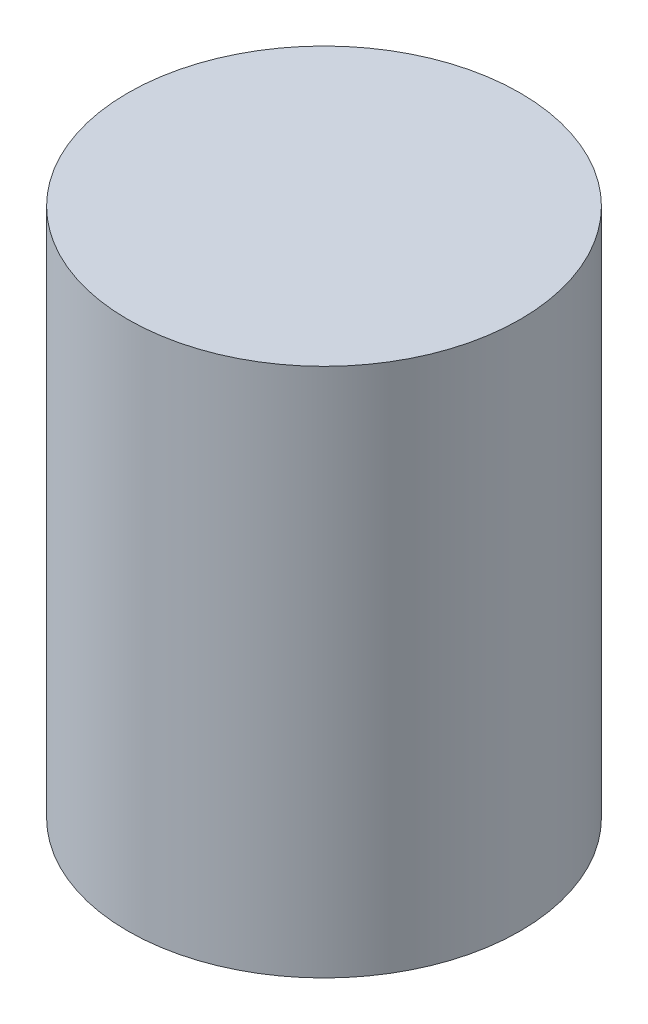
SolidWorks part; units mm, degrees
ref_plane "Спереди" through (0, 0, 0) normal (0, 0, 1) x (1, 0, 0)
ref_plane "Сверху" through (0, 0, 0) normal (0, 1, 0) x (1, 0, 0)
ref_plane "Справа" through (0, 0, 0) normal (1, 0, 0) x (0, 0, -1)
sketch "Эскиз1" plane through (0, 0, 0) normal (0, 1, 0) x (1, 0, 0)
  circle A0 centre (0, 0) radius 10
extrude "Бобышка-Вытянуть1" add sketch "Эскиз1" along normal blind 27
sketch "Эскиз2" plane through (0, 27, 0) normal (0, 1, 0) x (1, 0, 0)
  line L0 (0, -10) -> (0, 10)
  line L1 (0, 10) -> (-10, 0)
  line L2 (-10, 0) -> (10, 0)
  circle A0 centre (0, 0) radius 10 construction
